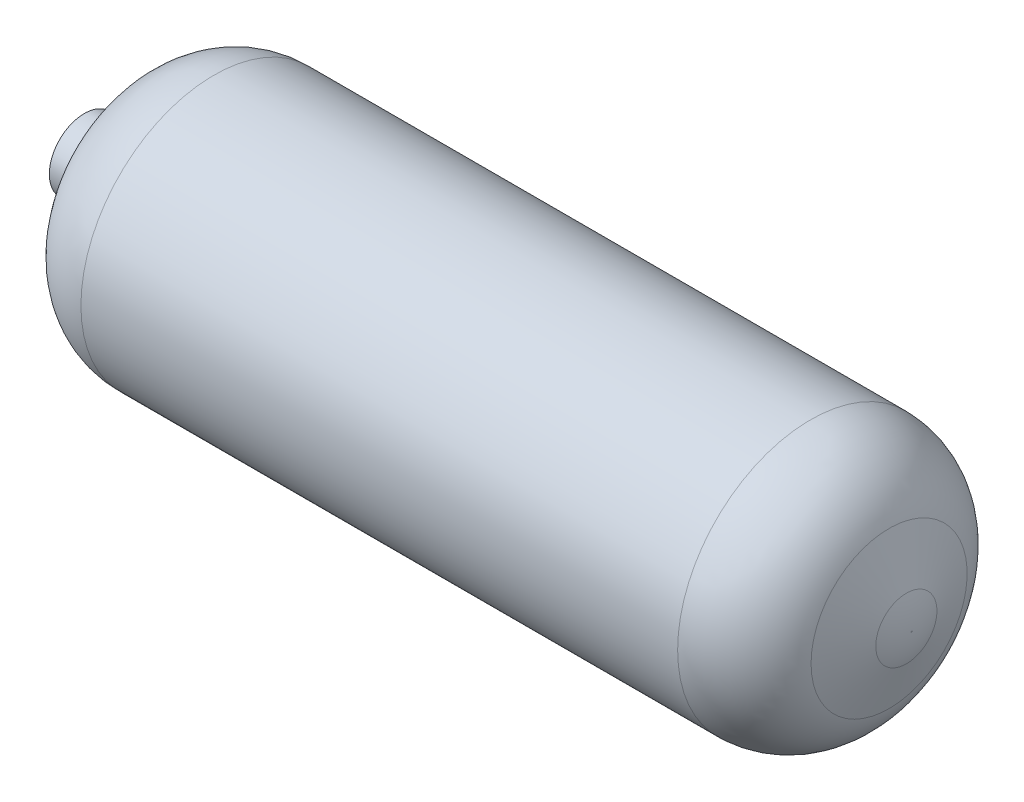
SolidWorks part; units mm, degrees
material "6061-T6 (SS)"
ref_plane "Front Plane" through (0, 0, 0) normal (0, 0, 1) x (1, 0, 0)
ref_plane "Top Plane" through (0, 0, 0) normal (0, 1, 0) x (1, 0, 0)
ref_plane "Right Plane" through (0, 0, 0) normal (1, 0, 0) x (0, 0, -1)
sketch "Sketch1" plane through (0, 0, 0) normal (0, 0, 1) x (1, 0, 0)
  line L0 (-0.2756, 0.129) -> (0.3032, 0.129)
  line L1 (-0.4012, 0.034) -> (-0.4012, 0)
  line L2 (-0.4012, 0.034) -> (-0.3773, 0.034)
  line L4 (-0.3729, 0.0367) -> (-0.3487, 0.0842)
  line L5 (-0.4012, 0) -> (0.4012, 0) construction
  line L6 (0.3794, 0.0757) -> (0.3961, 0.0297)
  line L7 (-0.4012, 0) -> (0.4012, 0)
  line L8 (0.4012, 0) -> (0.4012, 0.0006)
  arc A0 (-0.2756, 0.129) -> (-0.3487, 0.0842) centre (-0.2756, 0.047) ccw
  arc A1 (0.3032, 0.129) -> (0.3794, 0.0757) centre (0.3032, 0.048) cw
  arc A2 (0.4012, 0.0006) -> (0.3961, 0.0297) centre (0.3163, 0.0006) ccw
  arc A3 (-0.3729, 0.0367) -> (-0.3773, 0.034) centre (-0.3773, 0.039) cw
  point P6 (-0.3742, 0.034)
  dimension "D8" = 0.082
  dimension "D11" = 0.081
  dimension "D13" = 0.085
  dimension "D6" = 0.005
  dimension "D2" = 0.2756
  dimension "D3" = 0.034
  dimension "D4" = 0.3032
  dimension "D5" = 0.027
  dimension "D7" = 117
  dimension "D9" = 0.8025
  dimension "D10" = 110
revolve "Revolve2" add sketch "Sketch1" angle 360 about L7
scale "Scale1" scale about origin uniform scaling yes scale factor 649.767462
shell "Shell2" thickness 5.588
